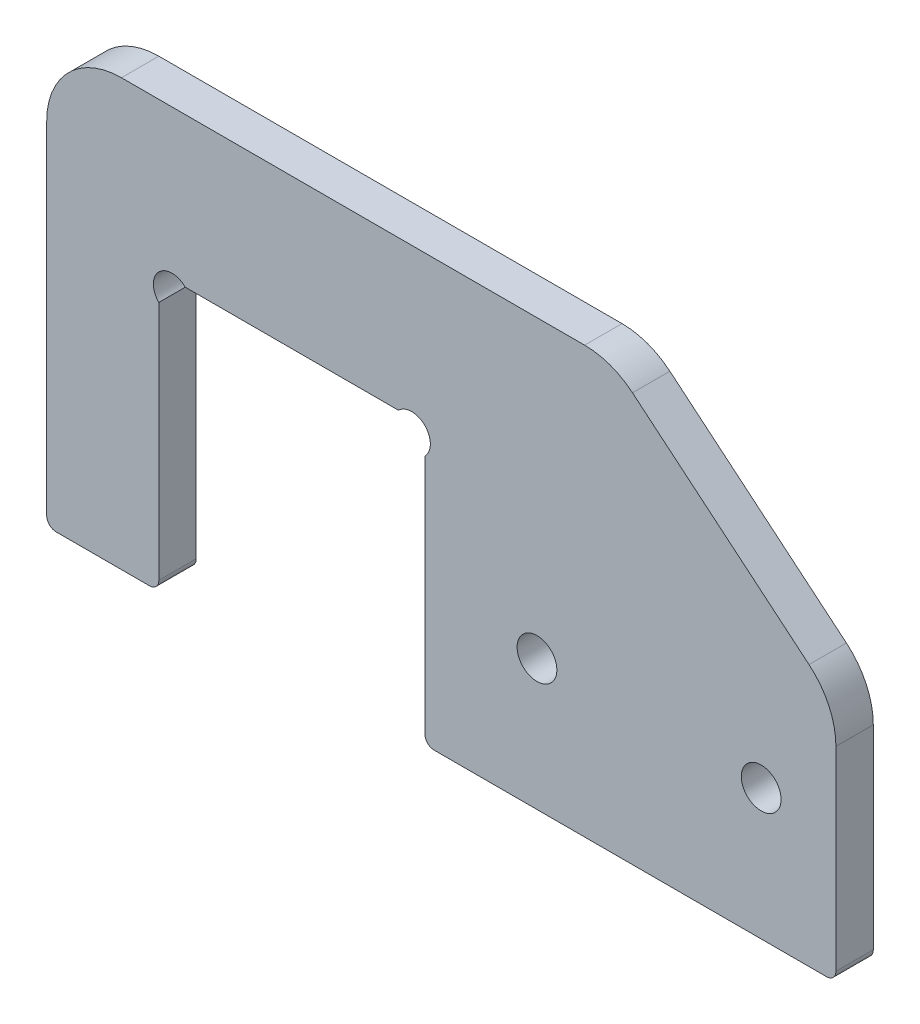
SolidWorks part; units mm, degrees
material "PC High Viscosity"
ref_plane "Front Plane" through (0, 0, 0) normal (0, 0, 1) x (1, 0, 0)
ref_plane "Top Plane" through (0, 0, 0) normal (0, 1, 0) x (1, 0, 0)
ref_plane "Right Plane" through (0, 0, 0) normal (1, 0, 0) x (0, 0, -1)
sketch "Sketch3" plane through (0, 0, 0) normal (0, 0, 1) x (1, 0, 0)
  line L0 (0, 0) -> (0, 72.39)
  line L1 (0, 72.39) -> (-134.112, 72.39)
  line L2 (-134.112, 72.39) -> (-134.112, 0)
  line L3 (-134.112, 0) -> (-115.062, 0)
  line L4 (-115.062, 0) -> (-115.062, 46.99)
  line L5 (-115.062, 46.99) -> (-69.85, 46.99)
  line L6 (-69.85, 46.99) -> (-69.85, 0)
  line L7 (-69.85, 0) -> (0, 0)
  point P7 (-12.7, 22.225)
  point P10 (-50.8, 22.225)
  dimension "D1" = 22.225
  dimension "D2" = 38.1
  dimension "D3" = 19.05
  dimension "D4" = 19.05
  dimension "D5" = 45.212
  dimension "D6" = 25.4
  dimension "D7" = 12.7
  dimension "D8" = 46.99
extrude "Boss-Extrude1" add sketch "Sketch3" along normal blind 6.35
hole_wizard "1/4 Clearance Hole1" positions "Sketch4" profile "Sketch5" hole size "1/4" standard "ANSI Inch" end condition through all
sketch "Sketch4" plane through (0, 0, 6.35) normal (0, 0, 1) x (1, 0, 0)
  point P0 (-50.8, 22.225)
  point P3 (-12.7, 22.225)
sketch "Sketch5" plane through (-50.8, 22.225, 6.35) normal (1, 0, 0) x (0, -1, 0)
  line L0 (0, 0) -> (0, 6.35)
  line L1 (0, 6.35) -> (3.3782, 6.35)
  line L2 (3.3782, 6.35) -> (3.3782, 0)
  line L5 (3.3782, 0) -> (0, 0)
  line L11 (0, -6.35) -> (0, 107.95) construction
  dimension "Thru Hole Dia." = 6.7564
  dimension "Thru Hole Depth" = 6.35
sketch "Sketch6" plane through (0, 0, 6.35) normal (0, 0, 1) x (1, 0, 0)
  line L0 (0, 72.39) -> (0, 40.64)
  line L1 (0, 0) -> (0, 72.39) construction
  line L2 (0, 40.64) -> (-38.1, 72.39)
  line L3 (0, 72.39) -> (-134.112, 72.39) construction
  line L4 (-38.1, 72.39) -> (0, 72.39)
  dimension "D1" = 31.75
  dimension "D2" = 38.1
extrude "Cut-Extrude1" cut sketch "Sketch6" against normal through all
fillet "Fillet1" radius 1.5875 4 edges at (0, 0, 3.175) (-134.112, 0, 3.175) (-115.062, 0, 3.175) (-69.85, 0, 3.175)
fillet "Fillet2" radius 12.7 3 edges at (-134.112, 72.39, 3.175) (0, 40.64, 3.175) (-38.1, 72.39, 3.175)
sketch "Sketch7" plane through (0, 0, 6.35) normal (0, 0, 1) x (1, 0, 0)
  line L0 (-112.8169, 44.7449) -> (-115.062, 46.99) construction
  line L2 (-115.062, 46.99) -> (-69.85, 46.99) construction
  line L3 (-92.456, 46.99) -> (-92.456, 0) construction
  circle A0 centre (-112.8169, 44.7449) radius 3.175
  circle A1 centre (-72.0951, 44.7449) radius 3.175
  dimension "D1" = 6.35
  dimension "D2" = 45
extrude "Cut-Extrude2" cut sketch "Sketch7" against normal through all
